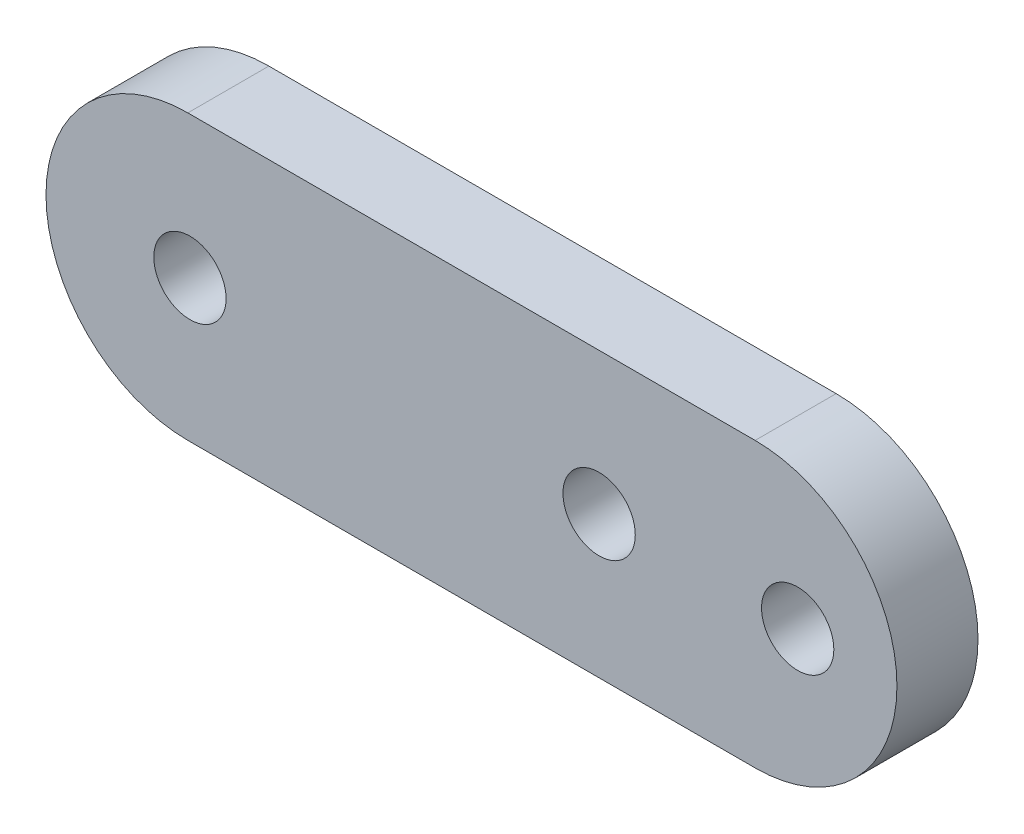
SolidWorks part; units mm, degrees
ref_plane "Front Plane" through (0, 0, 0) normal (0, 0, 1) x (1, 0, 0)
ref_plane "Top Plane" through (0, 0, 0) normal (0, 1, 0) x (1, 0, 0)
ref_plane "Right Plane" through (0, 0, 0) normal (1, 0, 0) x (0, 0, -1)
sketch "Sketch2" plane through (0, 0, 0) normal (0, 0, 1) x (1, 0, 0)
  line L0 (-20, 0) -> (20, 0) construction
  line L1 (-20, 10) -> (20, 10)
  line L2 (-20, -10) -> (20, -10)
  arc A0 (-20, 10) -> (-20, -10) centre (-20, 0) ccw
  arc A1 (20, -10) -> (20, 10) centre (20, 0) ccw
  point P2 (0, 0)
  dimension "D1" = 20
  dimension "D2" = 60
extrude "Boss-Extrude1" add sketch "Sketch2" along normal mid plane 5.715
sketch "Sketch3" plane through (0, 0, 2.8575) normal (0, 0, 1) x (1, 0, 0)
  line L0 (30, 0) -> (23, 0) construction
  line L1 (23, 0) -> (9, 0) construction
  arc A0 (20, -10) -> (20, 10) centre (20, 0) ccw construction
  circle A1 centre (9, 0) radius 2.55
  circle A2 centre (23, 0) radius 2.55
  dimension "D1" = 5.1
  dimension "D2" = 7
  dimension "D3" = 14
extrude "Cut-Extrude1" cut sketch "Sketch3" against normal through all
sketch "Sketch4" plane through (0, 0, 2.8575) normal (0, 0, 1) x (1, 0, 0)
  circle A0 centre (-19.85, 0) radius 2.55
  arc A3 (-20, 10) -> (-20, -10) centre (-20, 0) ccw construction
  dimension "D1" = 5.1
  dimension "D3" = 7.6
extrude "Cut-Extrude2" cut sketch "Sketch4" against normal up to surface (5.715 mm away) up to face at (11.55, 0, -2.8575)
equation "\"PullyHoldDiameter\"=5.1"
equation "\"D1@Sketch4\"=\"PullyHoldDiameter\""
equation "\"PullyPlateLength\"=60"
equation "\"D2@Sketch2\"=\"PullyPlateLength\""
